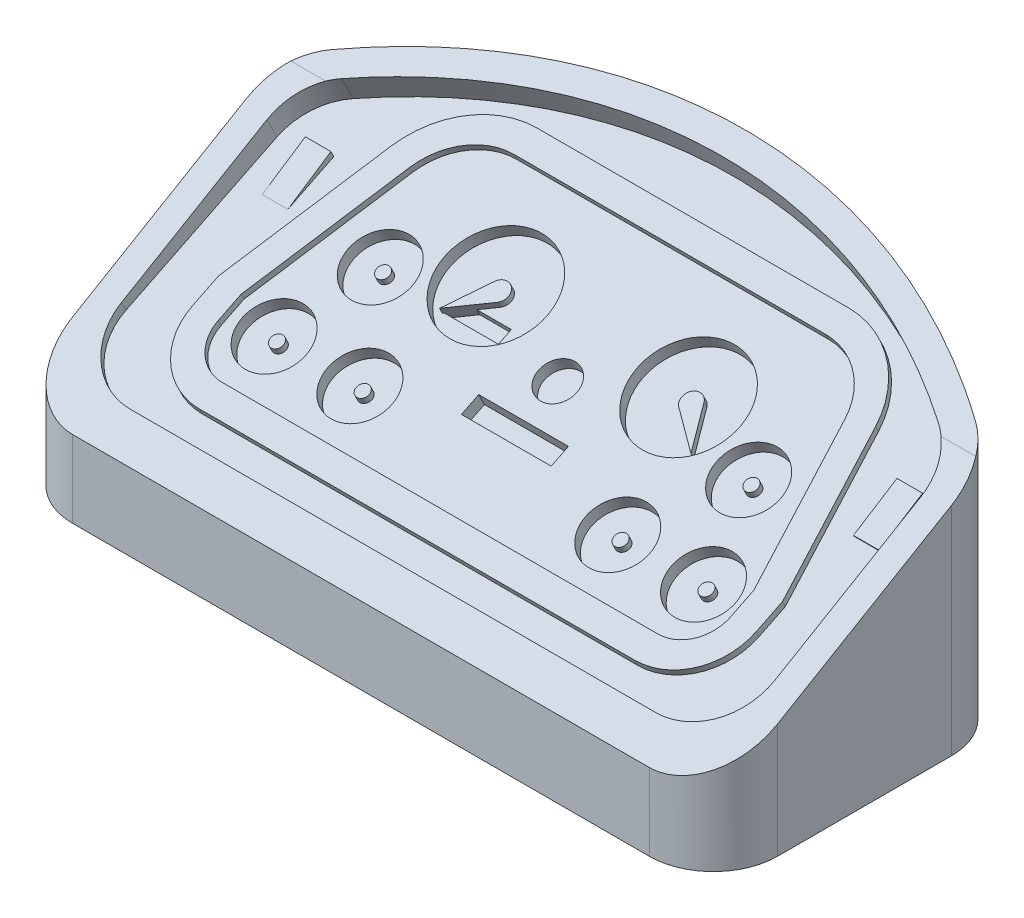
SolidWorks part; units mm, degrees
ref_plane "Front Plane" through (0, 0, 0) normal (0, 0, 1) x (1, 0, 0)
ref_plane "Top Plane" through (0, 0, 0) normal (0, 1, 0) x (1, 0, 0)
ref_plane "Right Plane" through (0, 0, 0) normal (1, 0, 0) x (0, 0, -1)
sketch "Sketch1" plane through (0, 0, 0) normal (0, 1, 0) x (1, 0, 0)
  line L2 (-27.5, 6.25) -> (-27.5, -15)
  line L3 (-27.5, -15) -> (27.5, -15)
  line L4 (27.5, 6.25) -> (27.5, -15)
  line L5 (-27.5, 15) -> (27.5, -15) construction
  line L6 (-27.5, -15) -> (27.5, 15) construction
  arc A0 (-27.5, 6.25) -> (27.5, 6.25) centre (0, -32.5893) cw
  point P0 (0, 0)
  dimension "D1" = 55
  dimension "D2" = 30
extrude "Boss-Extrude1" add sketch "Sketch1" along normal blind 25
sketch "Sketch2" plane through (27.5, 0, 0) normal (1, 0, 0) x (0, 0, -1)
  line L0 (-15, 8) -> (15, 22.8245)
  line L1 (15, 0) -> (15, 25) construction
  line L2 (15, 22.8245) -> (15, 25)
  line L3 (15, 25) -> (-15, 25)
  line L4 (-15, 25) -> (-15, 0) construction
  line L5 (-15, 25) -> (-15, 8)
  dimension "D1" = 8
extrude "Cut-Extrude1" cut sketch "Sketch2" against normal through all
sketch "Sketch3" plane through (0, 12.3874, 6.1213) normal (0, 0.8965, 0.443) x (1, 0, 0)
  line L6 (-25.5, 12.8175) -> (-25.5, -7.9036)
  line L7 (-25.5, -7.9036) -> (25.5, -7.9036)
  line L8 (25.5, -7.9036) -> (25.5, 12.8175)
  line L9 (-25.5, 10.2383) -> (-25.5, -7.9036)
  line L10 (-25.5, -7.9036) -> (25.5, -7.9036)
  line L11 (25.5, -7.9036) -> (25.5, 10.2383)
  arc A0 (25.5, 10.2383) -> (23.2697, 14.4011) centre (20.5, 10.2383) ccw
  arc A1 (-25.5, 10.2383) -> (-23.2697, 14.4011) centre (-20.5, 10.2383) cw
  spline S0 degree 3 poles (-863.9092, -2841.3645) (-189.098, -1165.4568) (180.5216, -70.0398) (17.7348, 17.5996) (15.6497, 18.5214) (12.9328, 19.4638) (12.3832, 19.6419) (11.2829, 19.9735) (10.731, 20.1273) (9.0705, 20.5537) (7.9569, 20.7909) (4.5963, 21.3623) (2.3297, 21.5573) (-1.1109, 21.5603) (-2.268, 21.5122) (-4.5523, 21.3201) (-5.6845, 21.1764) (-9.0519, 20.6063) (-11.2581, 20.0416) (-14.5097, 18.9184) (-15.5869, 18.4961) (-17.6888, 17.5725) (-18.717, 17.0703) (-323.1854, -146.6977) (1361.8392, -3848.7021) (-427.002, -1368.4987) knots -9.909364 -9.909364 -9.909364 -9.909364 0.125 0.125 0.25 0.25 0.28125 0.28125 0.3125 0.3125 0.375 0.375 0.5 0.5 0.5625 0.5625 0.625 0.625 0.75 0.75 0.8125 0.8125 0.875 0.875 19.723415 19.723415 19.723415 19.723415 only from (25.5, 12.8175) to (-25.5, 12.8175)
  spline S1 degree 3 poles (23.2697, 14.4011) (22.1222, 15.1646) (20.9449, 15.8713) (17.7348, 17.5996) (15.6497, 18.5214) (12.9328, 19.4638) (12.3832, 19.6419) (11.2829, 19.9735) (10.731, 20.1273) (9.0705, 20.5537) (7.9569, 20.7909) (4.5963, 21.3623) (2.3297, 21.5573) (-1.1109, 21.5603) (-2.268, 21.5122) (-4.5523, 21.3201) (-5.6845, 21.1764) (-9.0519, 20.6063) (-11.2581, 20.0416) (-14.5097, 18.9184) (-15.5869, 18.4961) (-17.6888, 17.5725) (-18.717, 17.0703) (-20.9371, 15.8762) (-22.1191, 15.1666) (-23.2697, 14.4011) knots 0.049661 0.049661 0.049661 0.049661 0.125 0.125 0.25 0.25 0.28125 0.28125 0.3125 0.3125 0.375 0.375 0.5 0.5 0.5625 0.5625 0.625 0.625 0.75 0.75 0.8125 0.8125 0.875 0.875 0.950394 0.950394 0.950394 0.950394
  dimension "D2" = 5
  dimension "D1" = 2
extrude "Cut-Extrude2" cut sketch "Sketch3" against normal blind 2
sketch "Sketch4" plane through (27.5, 0, 0) normal (1, 0, 0) x (0, 0, -1)
  line L0 (-15, 8) -> (-15, 6)
  line L1 (-15, 8) -> (-15, 0) construction
  line L5 (6.25, 18.5007) -> (-15, 8)
  line L6 (-15, 6) -> (6.25, 18.5007)
  dimension "D1" = 2
extrude "Cut-Extrude3" cut sketch "Sketch4" against normal through all
sketch "Sketch5" plane through (0, 10.5944, 5.2352) normal (0, 0.8965, 0.443) x (1, 0, 0)
  line L0 (-16.8747, -3.9036) -> (17.1253, -3.9036)
  line L1 (20.1253, -0.9036) -> (20.1253, 1.0964)
  line L2 (20.1253, 1.0964) -> (17.115, 12.3847)
  line L3 (12.2839, 16.0964) -> (-12.0333, 16.0964)
  line L4 (-16.8645, 12.3847) -> (-19.8747, 1.0964)
  line L5 (-19.8747, 1.0964) -> (-19.8747, -0.9036)
  line L6 (-25.5, -7.9036) -> (25.5, -7.9036) construction
  line L7 (-21.8747, 1.3585) -> (-21.8747, -0.9036)
  line L8 (-16.8747, -5.9036) -> (17.1253, -5.9036)
  line L9 (22.1253, -0.9036) -> (22.1253, 1.3585)
  line L10 (22.1253, 1.3585) -> (19.0475, 12.9)
  line L11 (12.2839, 18.0964) -> (-12.0333, 18.0964)
  line L12 (-18.797, 12.9) -> (-21.8747, 1.3585)
  arc A0 (17.115, 12.3847) -> (12.2839, 16.0964) centre (12.2839, 11.0964) ccw
  arc A1 (-12.0333, 16.0964) -> (-16.8645, 12.3847) centre (-12.0333, 11.0964) ccw
  arc A2 (17.1253, -3.9036) -> (20.1253, -0.9036) centre (17.1253, -0.9036) ccw
  arc A3 (-16.8747, -3.9036) -> (-19.8747, -0.9036) centre (-16.8747, -0.9036) cw
  arc A4 (-16.8747, -5.9036) -> (-21.8747, -0.9036) centre (-16.8747, -0.9036) cw
  arc A5 (17.1253, -5.9036) -> (22.1253, -0.9036) centre (17.1253, -0.9036) ccw
  arc A6 (19.0475, 12.9) -> (12.2839, 18.0964) centre (12.2839, 11.0964) ccw
  arc A7 (-12.0333, 18.0964) -> (-18.797, 12.9) centre (-12.0333, 11.0964) ccw
  point P8 (0, 0)
  point P9 (0, 0)
  point P12 (16.1253, 16.0964)
  point P15 (-15.8747, 16.0964)
  point P18 (20.1253, -3.9036)
  point P21 (-19.8747, -3.9036)
  dimension "D8" = 5
  dimension "D9" = 3
  dimension "D1" = 5
  dimension "D2" = 4
  dimension "D3" = 20
  dimension "D4" = 4
  dimension "D5" = 40
  dimension "D6" = 5
  dimension "D7" = 4
  dimension "D10" = 2
extrude "Boss-Extrude2" add sketch "Sketch5" along normal blind 0.5
fillet "Fillet2" radius 5 2 edges at (-27.5, 9.2504, -6.25) (27.5, 9.2504, -6.25)
fillet "Fillet4" radius 5 2 edges at (27.5, 3, 15) (-27.5, 3, 15)
fillet "Fillet5" radius 5 2 edges at (-25.5, 7.2801, 12.4134) (25.5, 7.2801, 12.4134)
sketch "Sketch6" plane through (0, 10.5944, 5.2352) normal (0, 0.8965, 0.443) x (1, 0, 0)
  line L0 (-16.8645, 12.3847) -> (-19.8747, 1.0964) construction
  line L1 (20.1253, 1.0964) -> (17.115, 12.3847) construction
  line L2 (12.2839, 16.0964) -> (-12.0333, 16.0964) construction
  line L3 (-16.8747, -3.9036) -> (17.1253, -3.9036) construction
  line L4 (-16.8747, -3.9036) -> (17.1253, -3.9036) construction
  line L5 (0.1253, 16.0964) -> (0.1253, -3.9036) construction
  line L7 (-3.3747, 3.1235) -> (3.6253, 3.1235)
  line L8 (-3.3747, 3.1235) -> (-3.3747, 1.622)
  line L9 (-3.3747, 1.622) -> (3.6253, 1.622)
  line L10 (3.6253, 3.1235) -> (3.6253, 1.622)
  circle A0 centre (-7.392, 9.0964) radius 4
  circle A1 centre (7.6425, 9.0964) radius 4
  circle A2 centre (-14.2462, 6.6793) radius 2.5
  circle A3 centre (-16.6263, 0.0964) radius 2.5
  circle A4 centre (-9.9337, 0.0964) radius 2.5
  circle A5 centre (10.1843, 0.0964) radius 2.5
  circle A6 centre (16.8769, 0.0964) radius 2.5
  circle A7 centre (14.4967, 6.6793) radius 2.5
  circle A8 centre (0.1253, 6.0964) radius 1.5
  dimension "D1" = 8
  dimension "D2" = 8
  dimension "D7" = 5
  dimension "D8" = 5
  dimension "D9" = 5
  dimension "D15" = 3
  dimension "D3" = 10
  dimension "D4" = 10
  dimension "D5" = 7
  dimension "D6" = 7
  dimension "D10" = 4
  dimension "D11" = 4
  dimension "D12" = 4
  dimension "D13" = 7
  dimension "D14" = 7.8697
  dimension "D16" = 7
  dimension "D17" = 3.5
extrude "Cut-Extrude4" cut sketch "Sketch6" against normal blind 1
sketch "Sketch7" plane through (0, 9.6979, 4.7922) normal (0, 0.8965, 0.443) x (1, 0, 0)
  line L0 (-7.392, 13.0964) -> (-7.392, 5.0964) construction
  line L1 (-8.0484, 9.4591) -> (-9.6818, 6.5028)
  line L2 (-9.6818, 6.5028) -> (-6.9507, 8.4899)
  line L3 (0.1253, 16.0964) -> (0.1253, -3.9036) construction
  line L4 (12.2839, 16.0964) -> (-12.0333, 16.0964) construction
  line L5 (-16.8747, -3.9036) -> (17.1253, -3.9036) construction
  line L6 (8.2989, 9.4591) -> (9.9324, 6.5028)
  line L7 (9.9324, 6.5028) -> (7.2012, 8.4899)
  circle A0 centre (-7.392, 9.0964) radius 4 construction
  circle A1 centre (-7.392, 9.0964) radius 4 construction
  arc A2 (-6.9507, 8.4899) -> (-8.0484, 9.4591) centre (-7.392, 9.0964) ccw
  arc A3 (7.2012, 8.4899) -> (8.2989, 9.4591) centre (7.6425, 9.0964) cw
  dimension "D1" = 1.5
extrude "Boss-Extrude3" add sketch "Sketch7" along normal blind 0.5
sketch "Sketch8" plane through (0, 9.6979, 4.7922) normal (0, 0.8965, 0.443) x (1, 0, 0)
  line L0 (0.1253, 16.0964) -> (0.1253, -3.9036) construction
  line L1 (12.2839, 16.0964) -> (-12.0333, 16.0964) construction
  line L2 (-16.8747, -3.9036) -> (17.1253, -3.9036) construction
  circle A0 centre (-14.2462, 6.6793) radius 0.5
  circle A1 centre (-16.6263, 0.0964) radius 0.5
  circle A2 centre (-9.9337, 0.0964) radius 0.5
  circle A3 centre (14.4967, 6.6793) radius 0.5
  circle A4 centre (10.1843, 0.0964) radius 0.5
  circle A5 centre (16.8769, 0.0964) radius 0.5
  dimension "D1" = 1
  dimension "D2" = 1
  dimension "D3" = 1
extrude "Boss-Extrude4" add sketch "Sketch8" along normal blind 0.5
sketch "Sketch9" plane through (0, 9.6979, 4.7922) normal (0, 0.8965, 0.443) x (1, 0, 0)
  line L0 (-9.6818, 6.5028) -> (-6.9507, 8.4899) construction
  line L1 (-9.5857, 6.5728) -> (-8.0492, 7.6907)
  line L2 (-5.3715, 7.6907) -> (-8.0492, 7.6907)
  line L3 (-5.3715, 7.6907) -> (-5.3715, 6.5728)
  line L4 (-5.3715, 6.5728) -> (-9.5857, 6.5728)
extrude "Cut-Extrude5" cut sketch "Sketch9" against normal blind 0.5
sketch "Sketch10" plane through (0, 10.5944, 5.2352) normal (0, 0.8965, 0.443) x (1, 0, 0)
  line L0 (25.5, -2.9036) -> (25.5, 10.2383) construction
  line L1 (-23.6604, 10.9064) -> (-21.6604, 10.9064)
  line L2 (-23.6604, 10.9064) -> (-23.6604, 6.9064)
  line L3 (-23.6604, 6.9064) -> (-21.6604, 6.9064)
  line L4 (-21.6604, 10.9064) -> (-21.6604, 6.9064)
  line L5 (22.5, 10.9064) -> (24.5, 10.9064)
  line L6 (22.5, 10.9064) -> (22.5, 6.9064)
  line L7 (22.5, 6.9064) -> (24.5, 6.9064)
  line L8 (24.5, 10.9064) -> (24.5, 6.9064)
  dimension "D1" = 2
  dimension "D2" = 4
  dimension "D3" = 2
  dimension "D4" = 4
  dimension "D5" = 1
extrude "Boss-Extrude5" add sketch "Sketch10" along normal blind 0.5
sketch "Sketch11" plane through (22.5, 0, 0) normal (-1, 0, 0) x (0, 0, 1)
  line L1 (-4.321, 15.8743) -> (-0.9236, 13.7205)
  line L2 (-0.7349, 14.1023) -> (-0.9564, 13.654) construction
  line L3 (-0.9236, 13.7205) -> (-0.7349, 14.1023)
  line L4 (-0.7349, 14.1023) -> (-4.321, 15.8743)
extrude "Cut-Extrude6" cut sketch "Sketch11" against normal up to surface (2 mm away) up to face at (24.5, 14.7642, -2.6387)
sketch "Sketch12" plane through (-23.6604, 0, 0) normal (-1, 0, 0) x (0, 0, 1)
  line L0 (-4.321, 15.8743) -> (-0.9564, 13.654)
  line L1 (-0.9564, 13.654) -> (-0.7349, 14.1023)
  line L2 (-0.7349, 14.1023) -> (-4.321, 15.8743)
extrude "Cut-Extrude7" cut sketch "Sketch12" against normal up to surface (2 mm away) up to face at (-21.6604, 14.7642, -2.6387)
